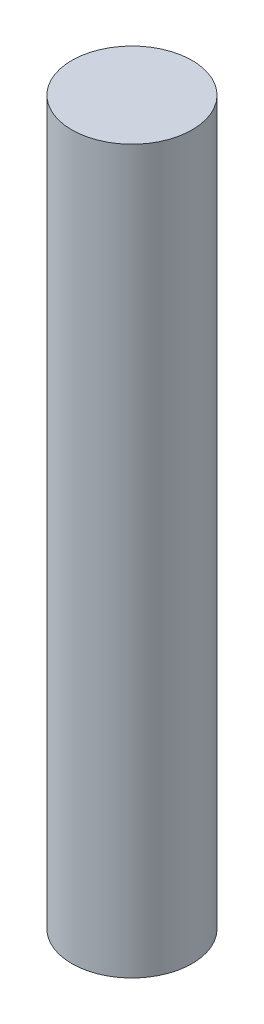
SolidWorks part; units mm, degrees
ref_plane "Front Plane" through (0, 0, 0) normal (0, 0, 1) x (1, 0, 0)
ref_plane "Top Plane" through (0, 0, 0) normal (0, 1, 0) x (1, 0, 0)
ref_plane "Right Plane" through (0, 0, 0) normal (1, 0, 0) x (0, 0, -1)
sketch "Sketch1" plane through (0, 0, 0) normal (0, 1, 0) x (1, 0, 0)
  circle A0 centre (0, 0) radius 5
  dimension "D1" = 10
extrude "Boss-Extrude1" add sketch "Sketch1" along normal blind 60
